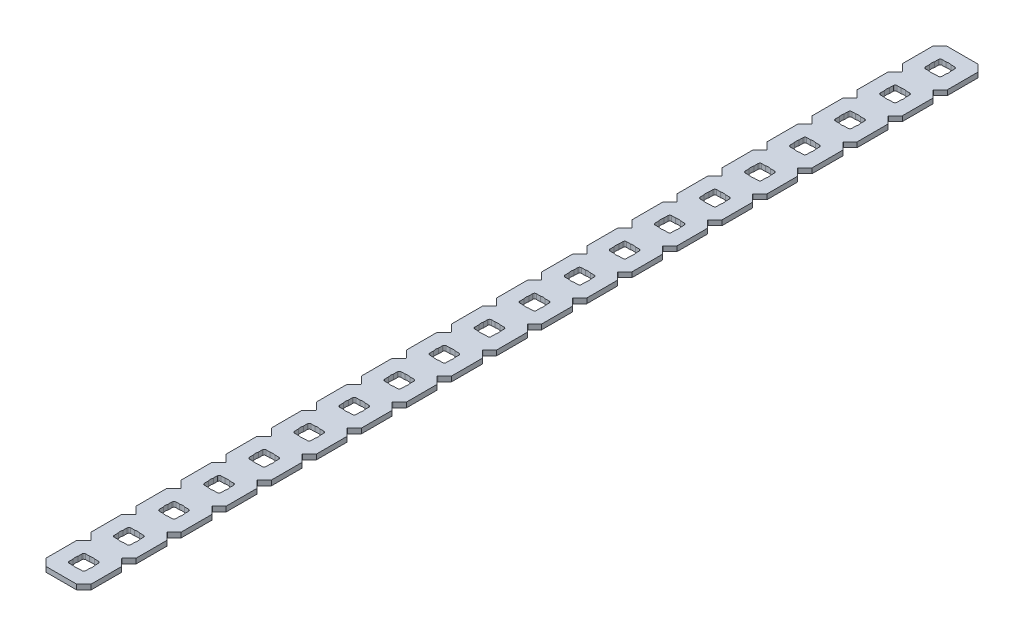
SolidWorks part; units mm, degrees
material "Custom Plastic"
ref_plane "Front Plane" through (0, 0, 0) normal (0, 0, 1) x (1, 0, 0)
ref_plane "Top Plane" through (0, 0, 0) normal (0, 1, 0) x (1, 0, 0)
ref_plane "Right Plane" through (0, 0, 0) normal (1, 0, 0) x (0, 0, -1)
ref_plane "Plane1" through (0, 0, 0) normal (0, -1, 0) x (1, 0, 0)
sketch "Sketch1" plane through (0, 0, 0) normal (0, -1, 0) x (1, 0, 0)
  line L0 (4.5466, -308.8386) -> (8.1534, -308.8386)
  line L1 (8.6614, -309.3466) -> (8.6614, -312.9534)
  line L2 (8.1534, -313.4614) -> (4.5466, -313.4614)
  line L3 (4.0386, -312.9534) -> (4.0386, -309.3466)
  line L4 (4.5466, -296.1386) -> (8.1534, -296.1386)
  line L5 (8.6614, -296.6466) -> (8.6614, -300.2534)
  line L6 (8.1534, -300.7614) -> (4.5466, -300.7614)
  line L7 (4.0386, -300.2534) -> (4.0386, -296.6466)
  line L8 (4.5466, -283.4386) -> (8.1534, -283.4386)
  line L9 (8.6614, -283.9466) -> (8.6614, -287.5534)
  line L10 (8.1534, -288.0614) -> (4.5466, -288.0614)
  line L11 (4.0386, -287.5534) -> (4.0386, -283.9466)
  line L12 (4.5466, -270.7386) -> (8.1534, -270.7386)
  line L13 (8.6614, -271.2466) -> (8.6614, -274.8534)
  line L14 (8.1534, -275.3614) -> (4.5466, -275.3614)
  line L15 (4.0386, -274.8534) -> (4.0386, -271.2466)
  line L16 (4.5466, -258.0386) -> (8.1534, -258.0386)
  line L17 (8.6614, -258.5466) -> (8.6614, -262.1534)
  line L18 (8.1534, -262.6614) -> (4.5466, -262.6614)
  line L19 (4.0386, -262.1534) -> (4.0386, -258.5466)
  line L20 (4.5466, -245.3386) -> (8.1534, -245.3386)
  line L21 (8.6614, -245.8466) -> (8.6614, -249.4534)
  line L22 (8.1534, -249.9614) -> (4.5466, -249.9614)
  line L23 (4.0386, -249.4534) -> (4.0386, -245.8466)
  line L24 (4.5466, -232.6386) -> (8.1534, -232.6386)
  line L25 (8.6614, -233.1466) -> (8.6614, -236.7534)
  line L26 (8.1534, -237.2614) -> (4.5466, -237.2614)
  line L27 (4.0386, -236.7534) -> (4.0386, -233.1466)
  line L28 (4.5466, -219.9386) -> (8.1534, -219.9386)
  line L29 (8.6614, -220.4466) -> (8.6614, -224.0534)
  line L30 (8.1534, -224.5614) -> (4.5466, -224.5614)
  line L31 (4.0386, -224.0534) -> (4.0386, -220.4466)
  line L32 (4.5466, -207.2386) -> (8.1534, -207.2386)
  line L33 (8.6614, -207.7466) -> (8.6614, -211.3534)
  line L34 (8.1534, -211.8614) -> (4.5466, -211.8614)
  line L35 (4.0386, -211.3534) -> (4.0386, -207.7466)
  line L36 (4.5466, -194.5386) -> (8.1534, -194.5386)
  line L37 (8.6614, -195.0466) -> (8.6614, -198.6534)
  line L38 (8.1534, -199.1614) -> (4.5466, -199.1614)
  line L39 (4.0386, -198.6534) -> (4.0386, -195.0466)
  line L40 (4.5466, -181.8386) -> (8.1534, -181.8386)
  line L41 (8.6614, -182.3466) -> (8.6614, -185.9534)
  line L42 (8.1534, -186.4614) -> (4.5466, -186.4614)
  line L43 (4.0386, -185.9534) -> (4.0386, -182.3466)
  line L44 (4.5466, -169.1386) -> (8.1534, -169.1386)
  line L45 (8.6614, -169.6466) -> (8.6614, -173.2534)
  line L46 (8.1534, -173.7614) -> (4.5466, -173.7614)
  line L47 (4.0386, -173.2534) -> (4.0386, -169.6466)
  line L48 (4.5466, -156.4386) -> (8.1534, -156.4386)
  line L49 (8.6614, -156.9466) -> (8.6614, -160.5534)
  line L50 (8.1534, -161.0614) -> (4.5466, -161.0614)
  line L51 (4.0386, -160.5534) -> (4.0386, -156.9466)
  line L52 (4.5466, -143.7386) -> (8.1534, -143.7386)
  line L53 (8.6614, -144.2466) -> (8.6614, -147.8534)
  line L54 (8.1534, -148.3614) -> (4.5466, -148.3614)
  line L55 (4.0386, -147.8534) -> (4.0386, -144.2466)
  line L56 (4.5466, -131.0386) -> (8.1534, -131.0386)
  line L57 (8.6614, -131.5466) -> (8.6614, -135.1534)
  line L58 (8.1534, -135.6614) -> (4.5466, -135.6614)
  line L59 (4.0386, -135.1534) -> (4.0386, -131.5466)
  line L60 (4.5466, -118.3386) -> (8.1534, -118.3386)
  line L61 (8.6614, -118.8466) -> (8.6614, -122.4534)
  line L62 (8.1534, -122.9614) -> (4.5466, -122.9614)
  line L63 (4.0386, -122.4534) -> (4.0386, -118.8466)
  line L64 (4.5466, -105.6386) -> (8.1534, -105.6386)
  line L65 (8.6614, -106.1466) -> (8.6614, -109.7534)
  line L66 (8.1534, -110.2614) -> (4.5466, -110.2614)
  line L67 (4.0386, -109.7534) -> (4.0386, -106.1466)
  line L68 (4.5466, -92.9386) -> (8.1534, -92.9386)
  line L69 (8.6614, -93.4466) -> (8.6614, -97.0534)
  line L70 (8.1534, -97.5614) -> (4.5466, -97.5614)
  line L71 (4.0386, -97.0534) -> (4.0386, -93.4466)
  line L72 (4.5466, -80.2386) -> (8.1534, -80.2386)
  line L73 (8.6614, -80.7466) -> (8.6614, -84.3534)
  line L74 (8.1534, -84.8614) -> (4.5466, -84.8614)
  line L75 (4.0386, -84.3534) -> (4.0386, -80.7466)
  line L76 (4.5466, -67.5386) -> (8.1534, -67.5386)
  line L77 (8.6614, -68.0466) -> (8.6614, -71.6534)
  line L78 (8.1534, -72.1614) -> (4.5466, -72.1614)
  line L79 (4.0386, -71.6534) -> (4.0386, -68.0466)
  line L80 (4.5466, -54.8386) -> (8.1534, -54.8386)
  line L81 (8.6614, -55.3466) -> (8.6614, -58.9534)
  line L82 (8.1534, -59.4614) -> (4.5466, -59.4614)
  line L83 (4.0386, -58.9534) -> (4.0386, -55.3466)
  line L84 (4.5466, -42.1386) -> (8.1534, -42.1386)
  line L85 (8.6614, -42.6466) -> (8.6614, -46.2534)
  line L86 (8.1534, -46.7614) -> (4.5466, -46.7614)
  line L87 (4.0386, -46.2534) -> (4.0386, -42.6466)
  line L88 (4.5466, -29.4386) -> (8.1534, -29.4386)
  line L89 (8.6614, -29.9466) -> (8.6614, -33.5534)
  line L90 (8.1534, -34.0614) -> (4.5466, -34.0614)
  line L91 (4.0386, -33.5534) -> (4.0386, -29.9466)
  line L92 (12.7, -302.773) -> (12.7, -294.127)
  line L93 (12.7, -294.127) -> (10.7628, -292.1898)
  line L94 (10.7628, -292.0102) -> (12.7, -290.073)
  line L95 (12.7, -290.073) -> (12.7, -281.427)
  line L96 (12.7, -281.427) -> (10.7628, -279.4898)
  line L97 (10.7628, -279.3102) -> (12.7, -277.373)
  line L98 (12.7, -277.373) -> (12.7, -268.727)
  line L99 (12.7, -268.727) -> (10.7628, -266.7898)
  line L100 (10.7628, -266.6102) -> (12.7, -264.673)
  line L101 (12.7, -264.673) -> (12.7, -256.027)
  line L102 (12.7, -256.027) -> (10.7628, -254.0898)
  line L103 (10.7628, -253.9102) -> (12.7, -251.973)
  line L104 (12.7, -251.973) -> (12.7, -243.327)
  line L105 (12.7, -243.327) -> (10.7628, -241.3898)
  line L106 (10.7628, -241.2102) -> (12.7, -239.273)
  line L107 (12.7, -239.273) -> (12.7, -230.627)
  line L108 (12.7, -230.627) -> (10.7628, -228.6898)
  line L109 (10.7628, -228.5102) -> (12.7, -226.573)
  line L110 (12.7, -226.573) -> (12.7, -217.927)
  line L111 (12.7, -217.927) -> (10.7628, -215.9898)
  line L112 (10.7628, -215.8102) -> (12.7, -213.873)
  line L113 (12.7, -213.873) -> (12.7, -205.227)
  line L114 (12.7, -205.227) -> (10.7628, -203.2898)
  line L115 (10.7628, -203.1102) -> (12.7, -201.173)
  line L116 (12.7, -201.173) -> (12.7, -192.527)
  line L117 (12.7, -192.527) -> (10.7628, -190.5898)
  line L118 (10.7628, -190.4102) -> (12.7, -188.473)
  line L119 (12.7, -188.473) -> (12.7, -179.827)
  line L120 (12.7, -179.827) -> (10.7628, -177.8898)
  line L121 (10.7628, -177.7102) -> (12.7, -175.773)
  line L122 (12.7, -175.773) -> (12.7, -167.127)
  line L123 (12.7, -167.127) -> (10.7628, -165.1898)
  line L124 (10.7628, -165.0102) -> (12.7, -163.073)
  line L125 (12.7, -163.073) -> (12.7, -154.427)
  line L126 (12.7, -154.427) -> (10.7628, -152.4898)
  line L127 (10.7628, -152.3102) -> (12.7, -150.373)
  line L128 (12.7, -150.373) -> (12.7, -141.727)
  line L129 (12.7, -141.727) -> (10.7628, -139.7898)
  line L130 (10.7628, -139.6102) -> (12.7, -137.673)
  line L131 (12.7, -137.673) -> (12.7, -129.027)
  line L132 (12.7, -129.027) -> (10.7628, -127.0898)
  line L133 (10.7628, -126.9102) -> (12.7, -124.973)
  line L134 (12.7, -124.973) -> (12.7, -116.327)
  line L135 (12.7, -116.327) -> (10.7628, -114.3898)
  line L136 (10.7628, -114.2102) -> (12.7, -112.273)
  line L137 (12.7, -112.273) -> (12.7, -103.627)
  line L138 (12.7, -103.627) -> (10.7628, -101.6898)
  line L139 (10.7628, -101.5102) -> (12.7, -99.573)
  line L140 (12.7, -99.573) -> (12.7, -90.927)
  line L141 (12.7, -90.927) -> (10.7628, -88.9898)
  line L142 (10.7628, -88.8102) -> (12.7, -86.873)
  line L143 (12.7, -86.873) -> (12.7, -78.227)
  line L144 (12.7, -78.227) -> (10.7628, -76.2898)
  line L145 (10.7628, -76.1102) -> (12.7, -74.173)
  line L146 (12.7, -74.173) -> (12.7, -65.527)
  line L147 (12.7, -65.527) -> (10.7628, -63.5898)
  line L148 (10.7628, -63.4102) -> (12.7, -61.473)
  line L149 (12.7, -61.473) -> (12.7, -52.827)
  line L150 (12.7, -52.827) -> (10.7628, -50.8898)
  line L151 (10.7628, -50.7102) -> (12.7, -48.773)
  line L152 (12.7, -48.773) -> (12.7, -40.127)
  line L153 (12.7, -40.127) -> (10.7628, -38.1898)
  line L154 (10.7628, -38.0102) -> (12.7, -36.073)
  line L155 (12.7, -36.073) -> (12.7, -27.427)
  line L156 (12.7, -27.427) -> (10.7628, -25.4898)
  line L157 (10.7628, -25.3102) -> (12.7, -23.373)
  line L158 (12.7, -23.373) -> (12.7, -14.727)
  line L159 (12.7, -14.727) -> (10.7628, -12.7898)
  line L160 (10.7628, -12.6102) -> (12.7, -10.673)
  line L161 (12.7, -10.673) -> (12.7, -2.032)
  line L162 (12.7, -2.032) -> (10.668, 0)
  line L163 (10.668, 0) -> (2.032, 0)
  line L164 (2.032, 0) -> (0, -2.032)
  line L165 (0, -2.032) -> (0, -10.673)
  line L166 (0, -10.673) -> (1.9372, -12.6102)
  line L167 (1.9372, -12.7898) -> (0, -14.727)
  line L168 (0, -14.727) -> (0, -23.373)
  line L169 (0, -23.373) -> (1.9372, -25.3102)
  line L170 (1.9372, -25.4898) -> (0, -27.427)
  line L171 (0, -27.427) -> (0, -36.073)
  line L172 (0, -36.073) -> (1.9372, -38.0102)
  line L173 (1.9372, -38.1898) -> (0, -40.127)
  line L174 (0, -40.127) -> (0, -48.773)
  line L175 (0, -48.773) -> (1.9372, -50.7102)
  line L176 (1.9372, -50.8898) -> (0, -52.827)
  line L177 (0, -52.827) -> (0, -61.473)
  line L178 (0, -61.473) -> (1.9372, -63.4102)
  line L179 (1.9372, -63.5898) -> (0, -65.527)
  line L180 (0, -65.527) -> (0, -74.173)
  line L181 (0, -74.173) -> (1.9372, -76.1102)
  line L182 (1.9372, -76.2898) -> (0, -78.227)
  line L183 (0, -78.227) -> (0, -86.873)
  line L184 (0, -86.873) -> (1.9372, -88.8102)
  line L185 (1.9372, -88.9898) -> (0, -90.927)
  line L186 (0, -90.927) -> (0, -99.573)
  line L187 (0, -99.573) -> (1.9372, -101.5102)
  line L188 (1.9372, -101.6898) -> (0, -103.627)
  line L189 (0, -103.627) -> (0, -112.273)
  line L190 (0, -112.273) -> (1.9372, -114.2102)
  line L191 (1.9372, -114.3898) -> (0, -116.327)
  line L192 (0, -116.327) -> (0, -124.973)
  line L193 (0, -124.973) -> (1.9372, -126.9102)
  line L194 (1.9372, -127.0898) -> (0, -129.027)
  line L195 (0, -129.027) -> (0, -137.673)
  line L196 (0, -137.673) -> (1.9372, -139.6102)
  line L197 (1.9372, -139.7898) -> (0, -141.727)
  line L198 (0, -141.727) -> (0, -150.373)
  line L199 (0, -150.373) -> (1.9372, -152.3102)
  line L200 (1.9372, -152.4898) -> (0, -154.427)
  line L201 (0, -154.427) -> (0, -163.073)
  line L202 (0, -163.073) -> (1.9372, -165.0102)
  line L203 (1.9372, -165.1898) -> (0, -167.127)
  line L204 (0, -167.127) -> (0, -175.773)
  line L205 (0, -175.773) -> (1.9372, -177.7102)
  line L206 (1.9372, -177.8898) -> (0, -179.827)
  line L207 (0, -179.827) -> (0, -188.473)
  line L208 (0, -188.473) -> (1.9372, -190.4102)
  line L209 (1.9372, -190.5898) -> (0, -192.527)
  line L210 (0, -192.527) -> (0, -201.173)
  line L211 (0, -201.173) -> (1.9372, -203.1102)
  line L212 (1.9372, -203.2898) -> (0, -205.227)
  line L213 (0, -205.227) -> (0, -213.873)
  line L214 (0, -213.873) -> (1.9372, -215.8102)
  line L215 (1.9372, -215.9898) -> (0, -217.927)
  line L216 (0, -217.927) -> (0, -226.573)
  line L217 (0, -226.573) -> (1.9372, -228.5102)
  line L218 (1.9372, -228.6898) -> (0, -230.627)
  line L219 (0, -230.627) -> (0, -239.273)
  line L220 (0, -239.273) -> (1.9372, -241.2102)
  line L221 (1.9372, -241.3898) -> (0, -243.327)
  line L222 (0, -243.327) -> (0, -251.973)
  line L223 (0, -251.973) -> (1.9372, -253.9102)
  line L224 (1.9372, -254.0898) -> (0, -256.027)
  line L225 (0, -256.027) -> (0, -264.673)
  line L226 (0, -264.673) -> (1.9372, -266.6102)
  line L227 (1.9372, -266.7898) -> (0, -268.727)
  line L228 (0, -268.727) -> (0, -277.373)
  line L229 (0, -277.373) -> (1.9372, -279.3102)
  line L230 (1.9372, -279.4898) -> (0, -281.427)
  line L231 (0, -281.427) -> (0, -290.073)
  line L232 (0, -290.073) -> (1.9372, -292.0102)
  line L233 (1.9372, -292.1898) -> (0, -294.127)
  line L234 (0, -294.127) -> (0, -302.773)
  line L235 (0, -302.773) -> (1.9372, -304.7102)
  line L236 (1.9372, -304.8898) -> (0, -306.827)
  line L237 (0, -306.827) -> (0, -315.468)
  line L238 (0, -315.468) -> (2.032, -317.5)
  line L239 (2.032, -317.5) -> (10.668, -317.5)
  line L240 (10.668, -317.5) -> (12.7, -315.468)
  line L241 (12.7, -315.468) -> (12.7, -306.827)
  line L242 (12.7, -306.827) -> (10.7628, -304.8898)
  line L243 (10.7628, -304.7102) -> (12.7, -302.773)
  line L244 (8.1534, -8.6614) -> (4.5466, -8.6614)
  line L245 (4.0386, -8.1534) -> (4.0386, -4.5466)
  line L246 (4.5466, -4.0386) -> (8.1534, -4.0386)
  line L247 (8.6614, -4.5466) -> (8.6614, -8.1534)
  line L248 (4.0386, -20.8534) -> (4.0386, -17.2466)
  line L249 (4.5466, -16.7386) -> (8.1534, -16.7386)
  line L250 (8.6614, -17.2466) -> (8.6614, -20.8534)
  line L251 (8.1534, -21.3614) -> (4.5466, -21.3614)
  arc A0 (4.0386, -309.3466) -> (4.5466, -308.8386) centre (4.5466, -309.3466) cw
  arc A1 (8.1534, -308.8386) -> (8.6614, -309.3466) centre (8.1534, -309.3466) cw
  arc A2 (8.6614, -312.9534) -> (8.1534, -313.4614) centre (8.1534, -312.9534) cw
  arc A3 (4.5466, -313.4614) -> (4.0386, -312.9534) centre (4.5466, -312.9534) cw
  arc A4 (4.0386, -296.6466) -> (4.5466, -296.1386) centre (4.5466, -296.6466) cw
  arc A5 (8.1534, -296.1386) -> (8.6614, -296.6466) centre (8.1534, -296.6466) cw
  arc A6 (8.6614, -300.2534) -> (8.1534, -300.7614) centre (8.1534, -300.2534) cw
  arc A7 (4.5466, -300.7614) -> (4.0386, -300.2534) centre (4.5466, -300.2534) cw
  arc A8 (4.0386, -283.9466) -> (4.5466, -283.4386) centre (4.5466, -283.9466) cw
  arc A9 (8.1534, -283.4386) -> (8.6614, -283.9466) centre (8.1534, -283.9466) cw
  arc A10 (8.6614, -287.5534) -> (8.1534, -288.0614) centre (8.1534, -287.5534) cw
  arc A11 (4.5466, -288.0614) -> (4.0386, -287.5534) centre (4.5466, -287.5534) cw
  arc A12 (4.0386, -271.2466) -> (4.5466, -270.7386) centre (4.5466, -271.2466) cw
  arc A13 (8.1534, -270.7386) -> (8.6614, -271.2466) centre (8.1534, -271.2466) cw
  arc A14 (8.6614, -274.8534) -> (8.1534, -275.3614) centre (8.1534, -274.8534) cw
  arc A15 (4.5466, -275.3614) -> (4.0386, -274.8534) centre (4.5466, -274.8534) cw
  arc A16 (4.0386, -258.5466) -> (4.5466, -258.0386) centre (4.5466, -258.5466) cw
  arc A17 (8.1534, -258.0386) -> (8.6614, -258.5466) centre (8.1534, -258.5466) cw
  arc A18 (8.6614, -262.1534) -> (8.1534, -262.6614) centre (8.1534, -262.1534) cw
  arc A19 (4.5466, -262.6614) -> (4.0386, -262.1534) centre (4.5466, -262.1534) cw
  arc A20 (4.0386, -245.8466) -> (4.5466, -245.3386) centre (4.5466, -245.8466) cw
  arc A21 (8.1534, -245.3386) -> (8.6614, -245.8466) centre (8.1534, -245.8466) cw
  arc A22 (8.6614, -249.4534) -> (8.1534, -249.9614) centre (8.1534, -249.4534) cw
  arc A23 (4.5466, -249.9614) -> (4.0386, -249.4534) centre (4.5466, -249.4534) cw
  arc A24 (4.0386, -233.1466) -> (4.5466, -232.6386) centre (4.5466, -233.1466) cw
  arc A25 (8.1534, -232.6386) -> (8.6614, -233.1466) centre (8.1534, -233.1466) cw
  arc A26 (8.6614, -236.7534) -> (8.1534, -237.2614) centre (8.1534, -236.7534) cw
  arc A27 (4.5466, -237.2614) -> (4.0386, -236.7534) centre (4.5466, -236.7534) cw
  arc A28 (4.0386, -220.4466) -> (4.5466, -219.9386) centre (4.5466, -220.4466) cw
  arc A29 (8.1534, -219.9386) -> (8.6614, -220.4466) centre (8.1534, -220.4466) cw
  arc A30 (8.6614, -224.0534) -> (8.1534, -224.5614) centre (8.1534, -224.0534) cw
  arc A31 (4.5466, -224.5614) -> (4.0386, -224.0534) centre (4.5466, -224.0534) cw
  arc A32 (4.0386, -207.7466) -> (4.5466, -207.2386) centre (4.5466, -207.7466) cw
  arc A33 (8.1534, -207.2386) -> (8.6614, -207.7466) centre (8.1534, -207.7466) cw
  arc A34 (8.6614, -211.3534) -> (8.1534, -211.8614) centre (8.1534, -211.3534) cw
  arc A35 (4.5466, -211.8614) -> (4.0386, -211.3534) centre (4.5466, -211.3534) cw
  arc A36 (4.0386, -195.0466) -> (4.5466, -194.5386) centre (4.5466, -195.0466) cw
  arc A37 (8.1534, -194.5386) -> (8.6614, -195.0466) centre (8.1534, -195.0466) cw
  arc A38 (8.6614, -198.6534) -> (8.1534, -199.1614) centre (8.1534, -198.6534) cw
  arc A39 (4.5466, -199.1614) -> (4.0386, -198.6534) centre (4.5466, -198.6534) cw
  arc A40 (4.0386, -182.3466) -> (4.5466, -181.8386) centre (4.5466, -182.3466) cw
  arc A41 (8.1534, -181.8386) -> (8.6614, -182.3466) centre (8.1534, -182.3466) cw
  arc A42 (8.6614, -185.9534) -> (8.1534, -186.4614) centre (8.1534, -185.9534) cw
  arc A43 (4.5466, -186.4614) -> (4.0386, -185.9534) centre (4.5466, -185.9534) cw
  arc A44 (4.0386, -169.6466) -> (4.5466, -169.1386) centre (4.5466, -169.6466) cw
  arc A45 (8.1534, -169.1386) -> (8.6614, -169.6466) centre (8.1534, -169.6466) cw
  arc A46 (8.6614, -173.2534) -> (8.1534, -173.7614) centre (8.1534, -173.2534) cw
  arc A47 (4.5466, -173.7614) -> (4.0386, -173.2534) centre (4.5466, -173.2534) cw
  arc A48 (4.0386, -156.9466) -> (4.5466, -156.4386) centre (4.5466, -156.9466) cw
  arc A49 (8.1534, -156.4386) -> (8.6614, -156.9466) centre (8.1534, -156.9466) cw
  arc A50 (8.6614, -160.5534) -> (8.1534, -161.0614) centre (8.1534, -160.5534) cw
  arc A51 (4.5466, -161.0614) -> (4.0386, -160.5534) centre (4.5466, -160.5534) cw
  arc A52 (4.0386, -144.2466) -> (4.5466, -143.7386) centre (4.5466, -144.2466) cw
  arc A53 (8.1534, -143.7386) -> (8.6614, -144.2466) centre (8.1534, -144.2466) cw
  arc A54 (8.6614, -147.8534) -> (8.1534, -148.3614) centre (8.1534, -147.8534) cw
  arc A55 (4.5466, -148.3614) -> (4.0386, -147.8534) centre (4.5466, -147.8534) cw
  arc A56 (4.0386, -131.5466) -> (4.5466, -131.0386) centre (4.5466, -131.5466) cw
  arc A57 (8.1534, -131.0386) -> (8.6614, -131.5466) centre (8.1534, -131.5466) cw
  arc A58 (8.6614, -135.1534) -> (8.1534, -135.6614) centre (8.1534, -135.1534) cw
  arc A59 (4.5466, -135.6614) -> (4.0386, -135.1534) centre (4.5466, -135.1534) cw
  arc A60 (4.0386, -118.8466) -> (4.5466, -118.3386) centre (4.5466, -118.8466) cw
  arc A61 (8.1534, -118.3386) -> (8.6614, -118.8466) centre (8.1534, -118.8466) cw
  arc A62 (8.6614, -122.4534) -> (8.1534, -122.9614) centre (8.1534, -122.4534) cw
  arc A63 (4.5466, -122.9614) -> (4.0386, -122.4534) centre (4.5466, -122.4534) cw
  arc A64 (4.0386, -106.1466) -> (4.5466, -105.6386) centre (4.5466, -106.1466) cw
  arc A65 (8.1534, -105.6386) -> (8.6614, -106.1466) centre (8.1534, -106.1466) cw
  arc A66 (8.6614, -109.7534) -> (8.1534, -110.2614) centre (8.1534, -109.7534) cw
  arc A67 (4.5466, -110.2614) -> (4.0386, -109.7534) centre (4.5466, -109.7534) cw
  arc A68 (4.0386, -93.4466) -> (4.5466, -92.9386) centre (4.5466, -93.4466) cw
  arc A69 (8.1534, -92.9386) -> (8.6614, -93.4466) centre (8.1534, -93.4466) cw
  arc A70 (8.6614, -97.0534) -> (8.1534, -97.5614) centre (8.1534, -97.0534) cw
  arc A71 (4.5466, -97.5614) -> (4.0386, -97.0534) centre (4.5466, -97.0534) cw
  arc A72 (4.0386, -80.7466) -> (4.5466, -80.2386) centre (4.5466, -80.7466) cw
  arc A73 (8.1534, -80.2386) -> (8.6614, -80.7466) centre (8.1534, -80.7466) cw
  arc A74 (8.6614, -84.3534) -> (8.1534, -84.8614) centre (8.1534, -84.3534) cw
  arc A75 (4.5466, -84.8614) -> (4.0386, -84.3534) centre (4.5466, -84.3534) cw
  arc A76 (4.0386, -68.0466) -> (4.5466, -67.5386) centre (4.5466, -68.0466) cw
  arc A77 (8.1534, -67.5386) -> (8.6614, -68.0466) centre (8.1534, -68.0466) cw
  arc A78 (8.6614, -71.6534) -> (8.1534, -72.1614) centre (8.1534, -71.6534) cw
  arc A79 (4.5466, -72.1614) -> (4.0386, -71.6534) centre (4.5466, -71.6534) cw
  arc A80 (4.0386, -55.3466) -> (4.5466, -54.8386) centre (4.5466, -55.3466) cw
  arc A81 (8.1534, -54.8386) -> (8.6614, -55.3466) centre (8.1534, -55.3466) cw
  arc A82 (8.6614, -58.9534) -> (8.1534, -59.4614) centre (8.1534, -58.9534) cw
  arc A83 (4.5466, -59.4614) -> (4.0386, -58.9534) centre (4.5466, -58.9534) cw
  arc A84 (4.0386, -42.6466) -> (4.5466, -42.1386) centre (4.5466, -42.6466) cw
  arc A85 (8.1534, -42.1386) -> (8.6614, -42.6466) centre (8.1534, -42.6466) cw
  arc A86 (8.6614, -46.2534) -> (8.1534, -46.7614) centre (8.1534, -46.2534) cw
  arc A87 (4.5466, -46.7614) -> (4.0386, -46.2534) centre (4.5466, -46.2534) cw
  arc A88 (4.0386, -29.9466) -> (4.5466, -29.4386) centre (4.5466, -29.9466) cw
  arc A89 (8.1534, -29.4386) -> (8.6614, -29.9466) centre (8.1534, -29.9466) cw
  arc A90 (8.6614, -33.5534) -> (8.1534, -34.0614) centre (8.1534, -33.5534) cw
  arc A91 (4.5466, -34.0614) -> (4.0386, -33.5534) centre (4.5466, -33.5534) cw
  arc A92 (10.7628, -292.1898) -> (10.7628, -292.0102) centre (10.8526, -292.1) cw
  arc A93 (10.7628, -279.4898) -> (10.7628, -279.3102) centre (10.8526, -279.4) cw
  arc A94 (10.7628, -266.7898) -> (10.7628, -266.6102) centre (10.8526, -266.7) cw
  arc A95 (10.7628, -254.0898) -> (10.7628, -253.9102) centre (10.8526, -254) cw
  arc A96 (10.7628, -241.3898) -> (10.7628, -241.2102) centre (10.8526, -241.3) cw
  arc A97 (10.7628, -228.6898) -> (10.7628, -228.5102) centre (10.8526, -228.6) cw
  arc A98 (10.7628, -215.9898) -> (10.7628, -215.8102) centre (10.8526, -215.9) cw
  arc A99 (10.7628, -203.2898) -> (10.7628, -203.1102) centre (10.8526, -203.2) cw
  arc A100 (10.7628, -190.5898) -> (10.7628, -190.4102) centre (10.8526, -190.5) cw
  arc A101 (10.7628, -177.8898) -> (10.7628, -177.7102) centre (10.8526, -177.8) cw
  arc A102 (10.7628, -165.1898) -> (10.7628, -165.0102) centre (10.8526, -165.1) cw
  arc A103 (10.7628, -152.4898) -> (10.7628, -152.3102) centre (10.8526, -152.4) cw
  arc A104 (10.7628, -139.7898) -> (10.7628, -139.6102) centre (10.8526, -139.7) cw
  arc A105 (10.7628, -127.0898) -> (10.7628, -126.9102) centre (10.8526, -127) cw
  arc A106 (10.7628, -114.3898) -> (10.7628, -114.2102) centre (10.8526, -114.3) cw
  arc A107 (10.7628, -101.6898) -> (10.7628, -101.5102) centre (10.8526, -101.6) cw
  arc A108 (10.7628, -88.9898) -> (10.7628, -88.8102) centre (10.8526, -88.9) cw
  arc A109 (10.7628, -76.2898) -> (10.7628, -76.1102) centre (10.8526, -76.2) cw
  arc A110 (10.7628, -63.5898) -> (10.7628, -63.4102) centre (10.8526, -63.5) cw
  arc A111 (10.7628, -50.8898) -> (10.7628, -50.7102) centre (10.8526, -50.8) cw
  arc A112 (10.7628, -38.1898) -> (10.7628, -38.0102) centre (10.8526, -38.1) cw
  arc A113 (10.7628, -25.4898) -> (10.7628, -25.3102) centre (10.8526, -25.4) cw
  arc A114 (10.7628, -12.7898) -> (10.7628, -12.6102) centre (10.8526, -12.7) cw
  arc A115 (1.9372, -12.6102) -> (1.9372, -12.7898) centre (1.8474, -12.7) cw
  arc A116 (1.9372, -25.3102) -> (1.9372, -25.4898) centre (1.8474, -25.4) cw
  arc A117 (1.9372, -38.0102) -> (1.9372, -38.1898) centre (1.8474, -38.1) cw
  arc A118 (1.9372, -50.7102) -> (1.9372, -50.8898) centre (1.8474, -50.8) cw
  arc A119 (1.9372, -63.4102) -> (1.9372, -63.5898) centre (1.8474, -63.5) cw
  arc A120 (1.9372, -76.1102) -> (1.9372, -76.2898) centre (1.8474, -76.2) cw
  arc A121 (1.9372, -88.8102) -> (1.9372, -88.9898) centre (1.8474, -88.9) cw
  arc A122 (1.9372, -101.5102) -> (1.9372, -101.6898) centre (1.8474, -101.6) cw
  arc A123 (1.9372, -114.2102) -> (1.9372, -114.3898) centre (1.8474, -114.3) cw
  arc A124 (1.9372, -126.9102) -> (1.9372, -127.0898) centre (1.8474, -127) cw
  arc A125 (1.9372, -139.6102) -> (1.9372, -139.7898) centre (1.8474, -139.7) cw
  arc A126 (1.9372, -152.3102) -> (1.9372, -152.4898) centre (1.8474, -152.4) cw
  arc A127 (1.9372, -165.0102) -> (1.9372, -165.1898) centre (1.8474, -165.1) cw
  arc A128 (1.9372, -177.7102) -> (1.9372, -177.8898) centre (1.8474, -177.8) cw
  arc A129 (1.9372, -190.4102) -> (1.9372, -190.5898) centre (1.8474, -190.5) cw
  arc A130 (1.9372, -203.1102) -> (1.9372, -203.2898) centre (1.8474, -203.2) cw
  arc A131 (1.9372, -215.8102) -> (1.9372, -215.9898) centre (1.8474, -215.9) cw
  arc A132 (1.9372, -228.5102) -> (1.9372, -228.6898) centre (1.8474, -228.6) cw
  arc A133 (1.9372, -241.2102) -> (1.9372, -241.3898) centre (1.8474, -241.3) cw
  arc A134 (1.9372, -253.9102) -> (1.9372, -254.0898) centre (1.8474, -254) cw
  arc A135 (1.9372, -266.6102) -> (1.9372, -266.7898) centre (1.8474, -266.7) cw
  arc A136 (1.9372, -279.3102) -> (1.9372, -279.4898) centre (1.8474, -279.4) cw
  arc A137 (1.9372, -292.0102) -> (1.9372, -292.1898) centre (1.8474, -292.1) cw
  arc A138 (1.9372, -304.7102) -> (1.9372, -304.8898) centre (1.8474, -304.8) cw
  arc A139 (10.7628, -304.8898) -> (10.7628, -304.7102) centre (10.8526, -304.8) cw
  arc A140 (8.6614, -8.1534) -> (8.1534, -8.6614) centre (8.1534, -8.1534) cw
  arc A141 (4.5466, -8.6614) -> (4.0386, -8.1534) centre (4.5466, -8.1534) cw
  arc A142 (4.0386, -4.5466) -> (4.5466, -4.0386) centre (4.5466, -4.5466) cw
  arc A143 (8.1534, -4.0386) -> (8.6614, -4.5466) centre (8.1534, -4.5466) cw
  arc A144 (4.0386, -17.2466) -> (4.5466, -16.7386) centre (4.5466, -17.2466) cw
  arc A145 (8.1534, -16.7386) -> (8.6614, -17.2466) centre (8.1534, -17.2466) cw
  arc A146 (8.6614, -20.8534) -> (8.1534, -21.3614) centre (8.1534, -20.8534) cw
  arc A147 (4.5466, -21.3614) -> (4.0386, -20.8534) centre (4.5466, -20.8534) cw
extrude "Boss-Extrude1" add sketch "Sketch1" against normal blind 1.4224
sketch "Sketch2" plane through (0, 1.4224, 0) normal (0, 1, 0) x (1, 0, 0)
  line L0 (6.35, 4.0386) -> (6.35, 8.6614) construction
  line L1 (8.1534, 4.0386) -> (4.5466, 4.0386) construction
  line L2 (4.5466, 8.6614) -> (8.1534, 8.6614) construction
  circle A0 centre (6.35, 6.35) radius 2.413
  dimension "D1" = 4.826
extrude "Cut-Extrude1" cut sketch "Sketch2" against normal blind 2.54
pattern_linear "LPattern1" count 25 spacing 12.7 along (0, 0, -1) of "Cut-Extrude1"
sketch "Sketch3" plane through (0, 1.4224, 0) normal (0, 1, 0) x (1, 0, 0)
  line L0 (0, 256.027) -> (0, 264.673) construction
  line L1 (0, 317.5) -> (12.7, 317.5)
  line L2 (0, 317.5) -> (0, 253.9102)
  line L3 (0, 253.9102) -> (12.7, 253.9102)
  line L4 (12.7, 317.5) -> (12.7, 253.9102)
  line L5 (12.7, 264.673) -> (12.7, 256.027) construction
  line L6 (2.032, 317.5) -> (10.668, 317.5) construction
extrude "Cut-Extrude2" cut sketch "Sketch3" against normal through all
